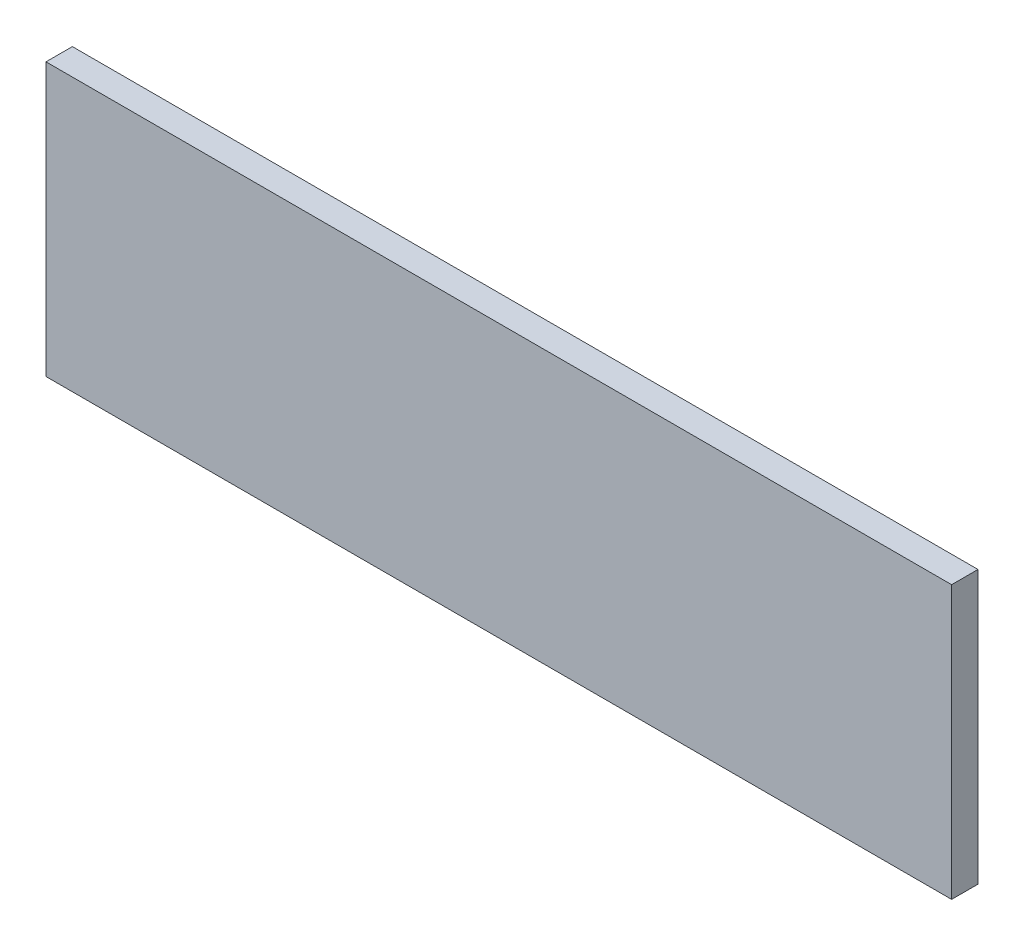
SolidWorks part; units mm, degrees
ref_plane "Plan de face" through (0, 0, 0) normal (0, 0, 1) x (1, 0, 0)
ref_plane "Plan de dessus" through (0, 0, 0) normal (0, 1, 0) x (1, 0, 0)
ref_plane "Plan de droite" through (0, 0, 0) normal (1, 0, 0) x (0, 0, -1)
sketch "Esquisse1" plane through (0, 0, 0) normal (0, 0, 1) x (1, 0, 0)
  line L1 (-51.5, 15.5) -> (51.5, 15.5)
  line L2 (-51.5, 15.5) -> (-51.5, -15.5)
  line L3 (-51.5, -15.5) -> (51.5, -15.5)
  line L4 (51.5, 15.5) -> (51.5, -15.5)
  line L5 (-51.5, 15.5) -> (51.5, -15.5) construction
  line L6 (-51.5, -15.5) -> (51.5, 15.5) construction
  point P0 (0, 0)
  dimension "D1" = 103
  dimension "D2" = 31
extrude "Boss.-Extru.1" add sketch "Esquisse1" along normal blind 3
